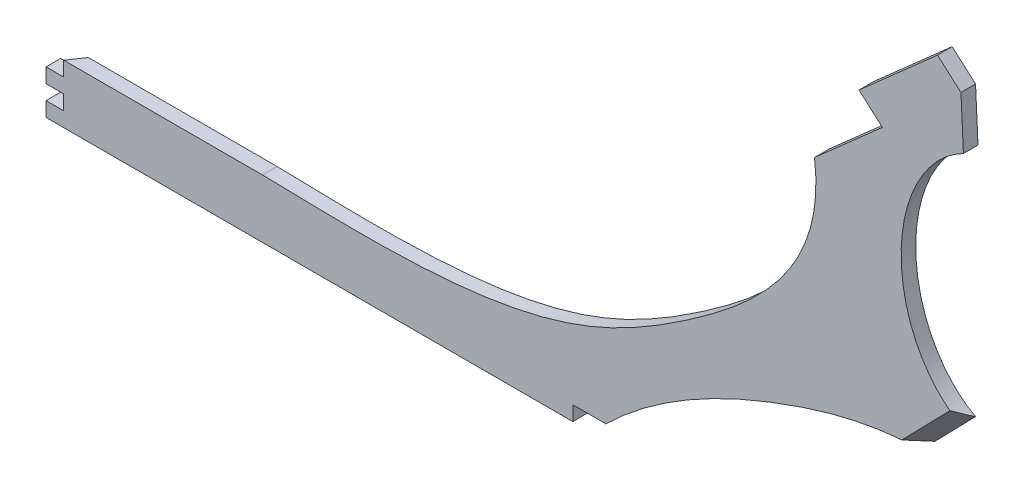
SolidWorks part; units mm, degrees
ref_plane "Front Plane" through (0, 0, 0) normal (0, 0, 1) x (1, 0, 0)
ref_plane "Top Plane" through (0, 0, 0) normal (0, 1, 0) x (1, 0, 0)
ref_plane "Right Plane" through (0, 0, 0) normal (1, 0, 0) x (0, 0, -1)
sketch "Sketch1" plane through (0, 0, 0) normal (0, 0, 1) x (1, 0, 0)
  line L0 (-427.1079, -118.0319) -> (-575.272, -118.0319)
  line L1 (-575.272, -118.0319) -> (-575.272, -158.0319)
  line L2 (-575.272, -158.0319) -> (-192.08, -158.0319)
  line L3 (-556.3198, -158.0319) -> (-202.6979, -158.0319) construction
  line L4 (-575.272, -118.0319) -> (-575.272, -158.0319) construction
  line L5 (-192.08, -158.0319) -> (-192.08, -148.0319)
  line L6 (50.9303, 169.8981) -> (61.8185, -59.5684)
  line L7 (50.9303, 169.8981) -> (34.9402, 184.0403)
  line L8 (34.9402, 184.0403) -> (-18.8626, 136.4553)
  line L9 (-18.8626, 136.4553) -> (-2.8725, 122.3131)
  line L10 (-2.8725, 122.3131) -> (-49.2705, 81.2772)
  spline S0 degree 3 poles (-192.08, -148.0319) (-157.837, -114.5188) (-75.1685, -70.6098) (16.2411, -49.9389) (61.8185, -59.5684) knots 0 0 0 0 0.513639 1 1 1 1
  spline S1 degree 3 poles (-202.6979, -158.0319) (-200.3571, -154.9452) (-197.889, -152.0073) (-192.7437, -146.3761) (-190.0663, -143.6831) (-184.5322, -138.5068) (-181.6754, -136.0237) (-175.8031, -131.2429) (-172.7877, -128.9453) (-166.6128, -124.5187) (-163.4533, -122.3896) (-158.6137, -119.3134) (-156.9837, -118.3076) (-153.6912, -116.3341) (-152.0315, -115.3682) (-143.6997, -110.6563) (-136.8987, -107.2419) (-123.0614, -101.0296) (-116.0248, -98.2325) (-101.7301, -93.2187) (-94.4718, -91.0021) (-83.4172, -88.1156) (-79.7043, -87.2267) (-74.0918, -86.0066) (-72.2125, -85.6185) (-68.457, -84.8842) (-66.5787, -84.5376) (-57.1849, -82.9066) (-49.6622, -81.9281) (-34.6005, -80.6566) (-27.0615, -80.3633) (-11.9655, -80.5416) (-4.4085, -81.0123) (6.9433, -82.4024) (10.7299, -82.9804) (16.4144, -84.0409) (18.3028, -84.4255) (22.0547, -85.2566) (23.9199, -85.7035) (33.1909, -88.1) (40.4322, -90.532) (49.221, -94.3425) (50.9656, -95.1434) (53.5614, -96.4063) (54.4232, -96.8375) (56.1396, -97.7211) (56.9949, -98.1739) (61.2311, -100.4802) (64.5052, -102.4676) (73.9722, -108.8698) (79.8111, -113.7232) (86.4632, -120.591) (87.7612, -122.0047) (90.2904, -124.9149) (91.5245, -126.4155) (95.0788, -130.9849) (97.2649, -134.1356) (103.3031, -143.8842) (106.6362, -150.7779) (109.3368, -158.0319) knots 0 0 0 0 0.03125 0.03125 0.0625 0.0625 0.09375 0.09375 0.125 0.125 0.15625 0.15625 0.171875 0.171875 0.1875 0.1875 0.25 0.25 0.3125 0.3125 0.375 0.375 0.40625 0.40625 0.421875 0.421875 0.4375 0.4375 0.5 0.5 0.5625 0.5625 0.625 0.625 0.65625 0.65625 0.671875 0.671875 0.6875 0.6875 0.75 0.75 0.765625 0.765625 0.773437 0.773437 0.78125 0.78125 0.8125 0.8125 0.875 0.875 0.890625 0.890625 0.90625 0.90625 0.9375 0.9375 1 1 1 1 construction
  spline S2 degree 3 poles (-427.1079, -118.0319) (-356.6403, -119.331) (-244.8705, -125.2196) (-108.6519, -44.2552) (-41.0572, 17.2026) (-49.2705, 81.2772) knots 0 0 0 0 0.468078 0.643593 1 1 1 1
  spline S4 degree 3 poles (-49.2705, 81.2772) (-48.1871, 71.274) (-48.3273, 61.3719) (-50.4807, 46.679) (-51.5227, 41.8082) (-54.2798, 32.122) (-55.9612, 27.4244) (-59.8662, 18.3038) (-62.0906, 13.8786) (-67.0356, 5.275) (-69.7563, 1.0965) (-75.6565, -7.0323) (-78.7862, -10.9151) (-85.3474, -18.3675) (-88.7797, -21.9378) (-95.9081, -28.8071) (-99.6043, -32.1061) (-107.2312, -38.463) (-111.1618, -41.521) (-117.2166, -45.9447) (-119.2553, -47.3876) (-123.3612, -50.2072) (-125.4299, -51.5851) (-131.6807, -55.6295) (-135.9071, -58.2066) (-148.7439, -65.6206) (-157.5111, -70.1421) (-175.3946, -78.4822) (-184.5114, -82.2999) (-198.4203, -87.5562) (-203.0958, -89.2295) (-210.1657, -91.6253) (-212.5295, -92.404) (-217.2604, -93.9193) (-219.6292, -94.6563) (-231.4888, -98.2408) (-241.0273, -100.7882) (-255.4077, -104.1506) (-260.2133, -105.1947) (-269.8491, -107.1284) (-274.6793, -108.0173) (-289.2054, -110.4607) (-298.9367, -111.7917) (-318.4791, -113.9504) (-328.2902, -114.7784) (-347.9725, -116.0545) (-357.8437, -116.5031) (-372.6783, -117.0004) (-377.6267, -117.137) (-387.5218, -117.3708) (-392.4698, -117.4681) (-407.3143, -117.7297) (-417.2114, -117.8644) (-427.1079, -118.0319) knots 0 0 0 0 0.0625 0.0625 0.09375 0.09375 0.125 0.125 0.15625 0.15625 0.1875 0.1875 0.21875 0.21875 0.25 0.25 0.28125 0.28125 0.3125 0.3125 0.328125 0.328125 0.34375 0.34375 0.375 0.375 0.4375 0.4375 0.5 0.5 0.53125 0.53125 0.546875 0.546875 0.5625 0.5625 0.625 0.625 0.65625 0.65625 0.6875 0.6875 0.75 0.75 0.8125 0.8125 0.875 0.875 0.90625 0.90625 0.9375 0.9375 1 1 1 1 construction
  dimension "D1" = 10
extrude "Boss-Extrude1" add sketch "Sketch1" along normal blind 10
ref_plane "Plane1" through (28.0045, -27.2589, 34.0591) normal (0.5402, -0.5258, 0.657) x (0.8415, 0.3376, -0.4218)
sketch "Sketch2" plane through (28.0045, -27.2589, 34.0591) normal (0.5402, -0.5258, 0.657) x (0.8415, 0.3376, -0.4218)
  line L0 (55.0969, -25.2819) -> (25.4033, -49.5066)
  line L1 (25.4033, -49.5066) -> (-27.1454, -41.5732)
  line L2 (-27.1454, -41.5732) -> (2.8882, -17.5317)
  line L3 (2.8882, -17.5317) -> (55.0969, -25.2819) construction
  line L4 (2.8882, -17.5317) -> (44.923, 24.503)
  line L5 (44.923, 24.503) -> (95.1824, 9.0003)
  line L6 (95.1824, 9.0003) -> (55.0969, -25.2819)
  spline S0 degree 3 poles (783.4693, -492.9431) (726.6575, -464.6342) (551.1892, -306.2374) (397.5951, -184.2435) (177.3328, -58.3121) (43.2885, -13.4414) (-44.6982, -16.3926) (-50.2164, -16.7063) knots 0 0 0 0 0.101495 0.305223 0.388807 0.52969 0.539121 0.539121 0.539121 0.539121 construction
  spline S1 degree 3 poles (783.4693, -492.9431) (726.6575, -464.6342) (551.1892, -306.2374) (397.5951, -184.2435) (177.3328, -58.3121) (37.4238, -11.4782) (-56.687, -16.9417) (-68.1591, -18.186) knots 0 0 0 0 0.101495 0.305223 0.388807 0.52969 0.549355 0.549355 0.549355 0.549355 construction
extrude "Cut-Extrude1" cut sketch "Sketch2" against normal mid plane 20
sketch "Sketch4" plane through (0, 0, 10) normal (0, 0, 1) x (1, 0, 0)
  line L2 (23.1319, -55.8032) -> (59.8499, -18.0808) construction
  ellipse E0 centre (76.4459, 53.1675) end of major axis (76.4459, -34.0073) minor radius 66.4535
  spline S3 degree 3 poles (681.9121, -142.394) (634.1035, -139.4694) (486.4424, -75.0336) (357.189, -31.6352) (171.8325, -7.667) (54.0954, -18.3293) (-25.1012, -54.3628) (-34.7553, -59.2068) knots 0 0 0 0 0.101495 0.305223 0.388807 0.52969 0.549355 0.549355 0.549355 0.549355 construction
  point P10 (50.8789, -27.2972)
extrude "Cut-Extrude2" cut sketch "Sketch4" against normal blind 10
ref_plane "Plane2" through (-379.0777, 0, -259.2075) normal (0.8255, 0, 0.5644) x (0.5644, 0, -0.8255)
sketch "Sketch5" plane through (-379.0777, 0, -259.2075) normal (0.8255, 0, 0.5644) x (0.5644, 0, -0.8255)
  line L0 (-314.0116, -118.0319) -> (-314.0116, -128.0319)
  line L1 (-314.0116, -118.0319) -> (-314.0116, -158.0319) construction
  line L2 (-184.7997, -118.0319) -> (-314.0116, -118.0319) construction
  line L4 (-314.0116, -118.0319) -> (-340.4502, -118.0319)
  line L5 (-340.4502, -118.0319) -> (-340.4502, -128.0319)
  line L8 (-249.3334, -118.0319) -> (-332.9638, -118.0319) construction
  line L9 (-314.0116, -128.0319) -> (-340.4502, -128.0319)
  line L10 (-314.0116, -138.0319) -> (-340.4502, -138.0319)
  line L11 (-314.0116, -148.0319) -> (-340.4502, -148.0319)
  line L12 (-340.4502, -138.0319) -> (-340.4502, -148.0319)
  line L13 (-314.0116, -138.0319) -> (-314.0116, -148.0319)
  dimension "D1" = 10
  dimension "D2" = 10
  dimension "D3" = 10
extrude "Cut-Extrude5" cut sketch "Sketch5" against normal blind 30
ref_plane "Plane3" through (-140.7549, 0, -266.7607) normal (0.4667, 0, 0.8844) x (0.8844, 0, -0.4667)
sketch "Sketch6" plane through (0, -158.0319, 0) normal (0, -1, 0) x (1, 0, 0)
  line L0 (-214.7038, 10) -> (-214.7038, 0)
  line L1 (-575.272, 10) -> (-192.08, 10) construction
  line L2 (-214.7038, 10) -> (-214.7038, 0) construction
  line L3 (-575.272, 0) -> (-192.08, 0) construction
  line L4 (-214.7038, 0) -> (-192.08, 0)
  line L5 (-192.08, 0) -> (-192.08, 10)
  line L6 (-192.08, 10) -> (-214.7038, 10)
extrude "Cut-Extrude6" cut sketch "Sketch6" against normal blind 10
